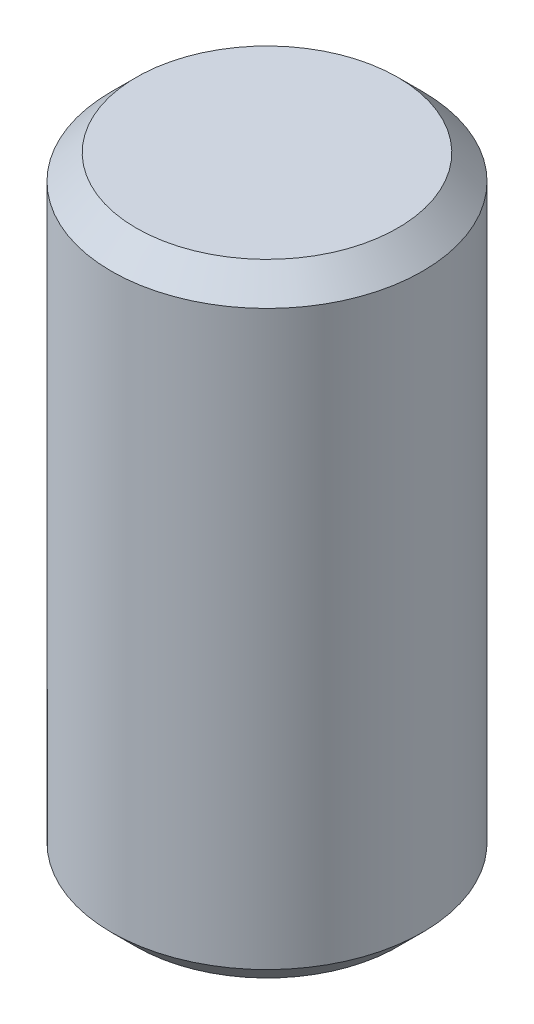
SolidWorks part; units mm, degrees
ref_plane "Front" through (0, 0, 0) normal (0, 0, 1) x (1, 0, 0)
ref_plane "Top" through (0, 0, 0) normal (0, 1, 0) x (1, 0, 0)
ref_plane "Right" through (0, 0, 0) normal (1, 0, 0) x (0, 0, -1)
sketch "Sketch1" plane through (0, 0, 0) normal (0, 0, 1) x (1, 0, 0)
  line L0 (0, 6.0802) -> (0, -6.0802) construction
  line L1 (0, -6.35) -> (3.175, -6.35)
  line L2 (3.175, -6.35) -> (3.175, 6.35)
  line L3 (3.175, 6.35) -> (0, 6.35)
  line L4 (0, 6.35) -> (0, -6.35)
  point P6 (0, 0)
  dimension "D1" = 6.35
  dimension "D2" = 12.7
revolve "Revolve1" add sketch "Sketch1" angle 360 about L0
chamfer "Chamfer1" distance 0.508 angle 45 2 edges at (0, -6.35, 3.175) (0, 6.35, 3.175)
